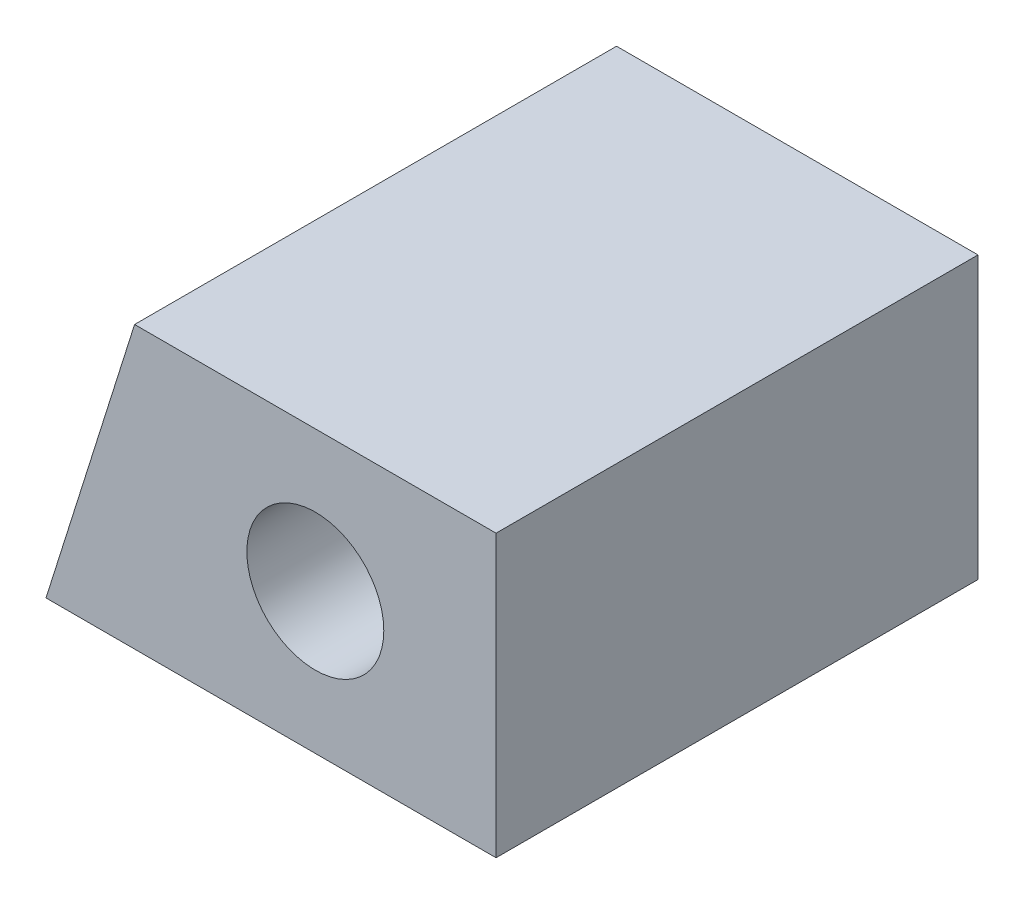
SolidWorks part; units mm, degrees
ref_plane "Front Plane" through (0, 0, 0) normal (0, 0, 1) x (1, 0, 0)
ref_plane "Top Plane" through (0, 0, 0) normal (0, 1, 0) x (1, 0, 0)
ref_plane "Right Plane" through (0, 0, 0) normal (1, 0, 0) x (0, 0, -1)
sketch "Sketch1" plane through (0, 0, 0) normal (0, 0, 1) x (1, 0, 0)
  line L0 (-3.3971, 3.5) -> (-5.6029, -3.5)
  line L1 (-5.6029, -3.5) -> (5.6029, -3.5)
  line L2 (5.6029, -3.5) -> (5.6029, 3.5)
  line L3 (5.6029, 3.5) -> (-3.3971, 3.5)
  circle A0 centre (1.1029, 0) radius 1.705
  dimension "D2" = 3.41
  dimension "D1" = 9
  dimension "D3" = 7
  dimension "D4" = 107.49
  dimension "D5" = 3.5
  dimension "D6" = 4.5
extrude "Boss-Extrude1" add sketch "Sketch1" along normal blind 12
